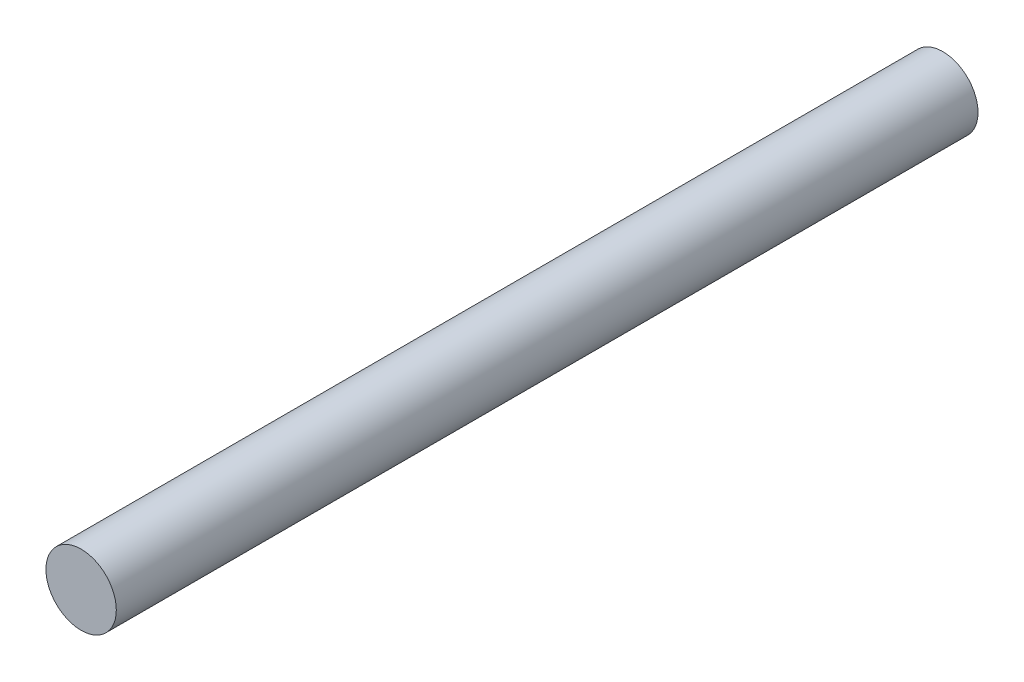
SolidWorks part; units mm, degrees
ref_plane "Front Plane" through (0, 0, 0) normal (0, 0, 1) x (1, 0, 0)
ref_plane "Top Plane" through (0, 0, 0) normal (0, 1, 0) x (1, 0, 0)
ref_plane "Right Plane" through (0, 0, 0) normal (1, 0, 0) x (0, 0, -1)
sketch "Sketch1" plane through (0, 0, 0) normal (0, 0, 1) x (1, 0, 0)
  circle A0 centre (0, 0) radius 2.45
extrude "Boss-Extrude1" add sketch "Sketch1" along normal blind 60
